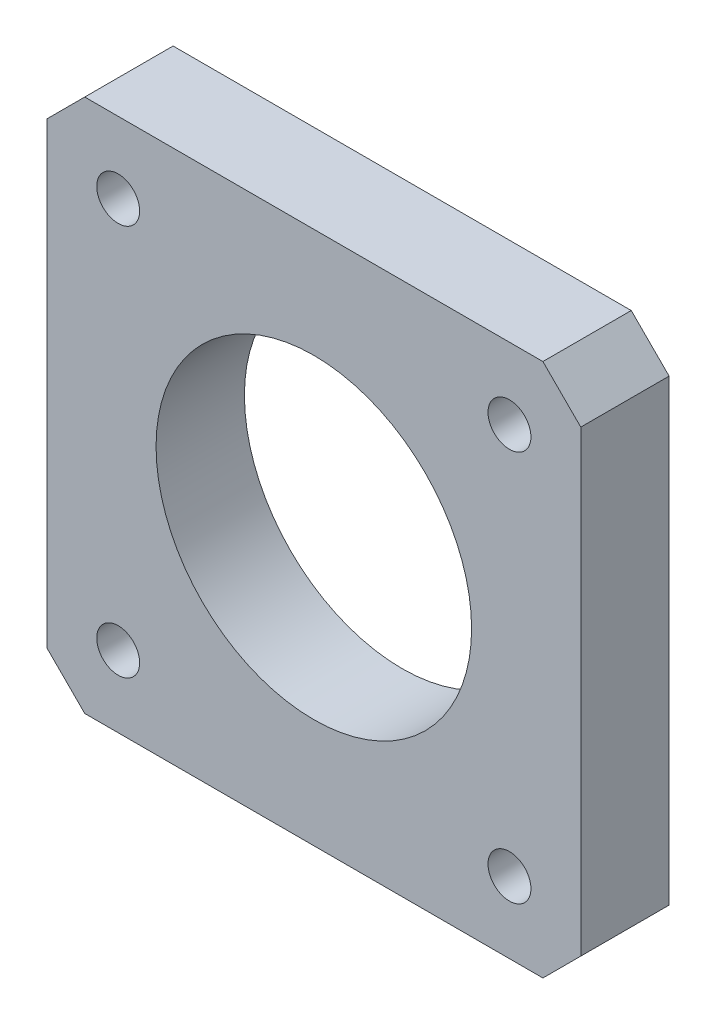
SolidWorks part; units mm, degrees
ref_plane "Front Plane" through (0, 0, 0) normal (0, 0, 1) x (1, 0, 0)
ref_plane "Top Plane" through (0, 0, 0) normal (0, 1, 0) x (1, 0, 0)
ref_plane "Right Plane" through (0, 0, 0) normal (1, 0, 0) x (0, 0, -1)
sketch "Sketch1" plane through (0, 0, 0) normal (0, 0, 1) x (1, 0, 0)
  line L1 (-21.15, -21.15) -> (21.15, -21.15)
  line L2 (-21.15, -21.15) -> (-21.15, 21.15)
  line L3 (-21.15, 21.15) -> (21.15, 21.15)
  line L4 (21.15, -21.15) -> (21.15, 21.15)
  line L5 (-21.15, -21.15) -> (21.15, 21.15) construction
  line L6 (-21.15, 21.15) -> (21.15, -21.15) construction
  circle A0 centre (0, 0) radius 12.5
  dimension "D1" = 42.3
  dimension "D3" = 25
  dimension "D2" = 42.3
extrude "Boss-Extrude1" add sketch "Sketch1" along normal blind 7
chamfer "Chamfer1" distance 3 angle 45 4 edges at (-21.15, -21.15, 3.5) (21.15, -21.15, 3.5) (-21.15, 21.15, 3.5) (21.15, 21.15, 3.5)
hole_wizard "M3 Clearance Hole1" positions "Sketch2" profile "Sketch3" hole size "M3" standard "ANSI Metric"
sketch "Sketch2" plane through (0, 0, 7) normal (0, 0, 1) x (1, 0, 0)
  line L0 (21.15, -18.15) -> (21.15, 18.15) construction
  line L1 (18.15, 21.15) -> (-18.15, 21.15) construction
  point P0 (15.5, 15.5)
  point P13 (-15.5, 15.5)
  point P14 (-15.5, -15.5)
  point P15 (15.5, -15.5)
  dimension "D1" = 5.65
  dimension "D2" = 5.65
  dimension "D3" = 2
  dimension "D4" = 2
sketch "Sketch3" plane through (15.5, 15.5, 7) normal (1, 0, 0) x (0, -1, 0)
  line L0 (0, 0) -> (0, 8.5215)
  line L1 (0, 8.5215) -> (1.7, 7.5)
  line L2 (1.7, 7.5) -> (1.7, 0)
  line L5 (1.7, 0) -> (0, 0)
  line L10 (0, 8.5215) -> (-1.7, 7.5) construction
  line L11 (0, -6.35) -> (0, 107.95) construction
  dimension "Hole Dia." = 3.4
  dimension "Hole Depth" = 7.5
  dimension "Drill Angle" = 118
